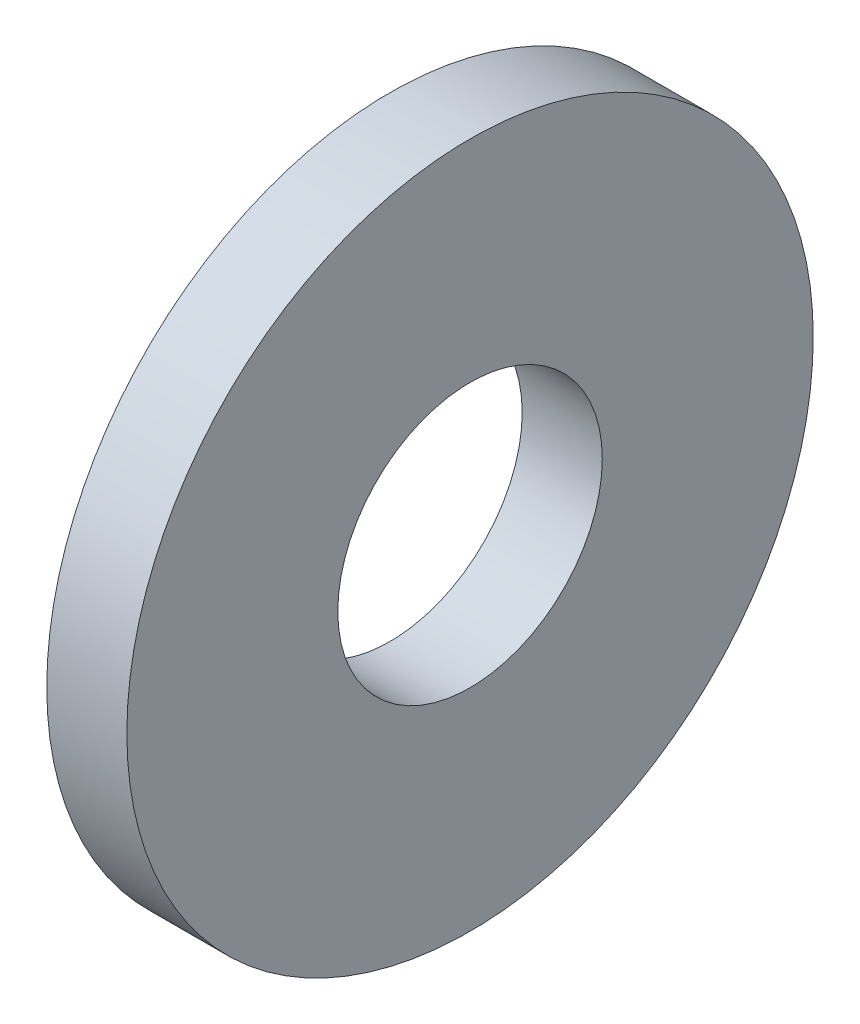
SolidWorks part; units mm, degrees
ref_plane "Plane1" through (0, 0, 0) normal (0, 0, 1) x (1, 0, 0)
ref_plane "Plane2" through (0, 0, 0) normal (0, 1, 0) x (1, 0, 0)
ref_plane "Plane3" through (0, 0, 0) normal (1, 0, 0) x (0, 0, -1)
sketch "Sketch1" plane through (0, 0, 0) normal (0, 0, 1) x (1, 0, 0)
  line L0 (-34.925, 0) -> (9.525, 0) construction
  line L1 (0, 2.89) -> (0, 7.5)
  line L2 (0, 7.5) -> (-1.75, 7.5)
  line L3 (-1.75, 7.5) -> (-1.75, 2.89)
  line L4 (-1.75, 2.89) -> (0, 2.89)
  dimension "Thickness" = 1.75
  dimension "Inside_dia" = 5.78
  dimension "Outside_dia" = 15
revolve "Base-Revolve" add sketch "Sketch1" angle 360 about L0
